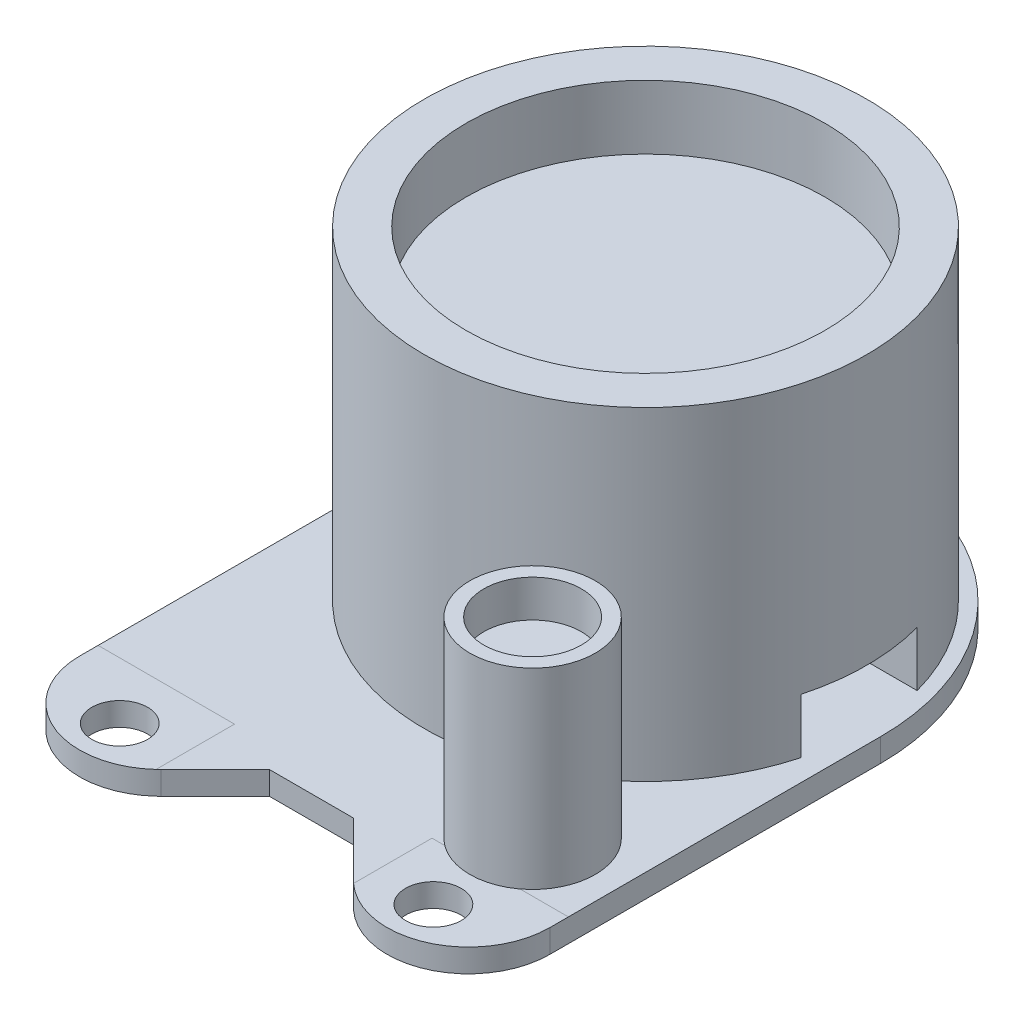
SolidWorks part; units mm, degrees
ref_plane "Front" through (0, 0, 0) normal (0, 0, 1) x (1, 0, 0)
ref_plane "Top" through (0, 0, 0) normal (0, 1, 0) x (1, 0, 0)
ref_plane "Right" through (0, 0, 0) normal (1, 0, 0) x (0, 0, -1)
sketch "Sketch1" plane through (0, 0, 0) normal (0, 1, 0) x (1, 0, 0)
  line L0 (-10.12, 0) -> (-10.12, -14.24)
  line L1 (10.12, 0) -> (10.12, -14.24)
  line L2 (-6.62, -17.74) -> (6.62, -17.74) construction
  line L3 (0, -0.8108) -> (0, -50000.8108) construction
  line L4 (-1.8103, -14.38) -> (1.8103, -14.38)
  line L5 (-4.1451, -16.7149) -> (-1.8103, -14.38)
  line L6 (1.8103, -14.38) -> (4.1451, -16.7149)
  arc A0 (10.12, 0) -> (-10.12, 0) centre (0, 0) ccw
  circle A1 centre (-6.75, -15.88) radius 1.2
  circle A2 centre (6.75, -15.88) radius 1.2
  arc A3 (-4.1451, -16.7149) -> (-10.12, -14.24) centre (-6.62, -14.24) cw
  arc A4 (4.1451, -16.7149) -> (10.12, -14.24) centre (6.62, -14.24) ccw
  dimension "D1" = 20.24
  dimension "D2" = 27.86
  dimension "D3" = 2.4
  dimension "D4" = 13.5
  dimension "D7" = 26
  dimension "D6" = 0.66
  dimension "D8" = 3.5
  dimension "D9" = 3.5
  dimension "D5" = 24.5
  dimension "D10" = 45
extrude "Boss-Extrude1" add sketch "Sketch1" along normal blind 1
sketch "Sketch2" plane through (0, 1, 0) normal (0, 1, 0) x (1, 0, 0)
  line L0 (0, 0) -> (0, -50000) construction
  line L1 (0, 0) -> (50000, 0) construction
  line L3 (10.12, -14.24) -> (10.12, 0) construction
  line L4 (-4.25, -13.44) -> (-10.12, -13.44)
  line L5 (10.12, -14.24) -> (10.12, -13.44)
  line L6 (4.25, -13.44) -> (4.25, -16.8155)
  line L7 (4.25, -13.44) -> (10.12, -13.44)
  line L8 (-4.25, -13.44) -> (-4.25, -16.8155)
  line L9 (-10.12, -14.24) -> (-10.12, -13.44)
  arc A0 (4.1451, -16.7149) -> (10.12, -14.24) centre (6.62, -14.24) ccw construction
  arc A1 (4.25, -16.8155) -> (10.12, -14.24) centre (6.62, -14.24) ccw
  arc A2 (-4.25, -16.8155) -> (-10.12, -14.24) centre (-6.62, -14.24) cw
  dimension "D2" = 4.3
  dimension "D1" = 8.5
split line "Split Line1"
sketch "Sketch3" plane through (0, 0, 0) normal (0, -1, 0) x (1, 0, 0)
  line L0 (0, 0) -> (50000, 0) construction
  line L1 (0, 0) -> (3.75, 0) construction
  line L2 (0, 0) -> (2.6517, -2.6517) construction
  circle A0 centre (0, 0) radius 4.25
  circle A1 centre (0, 0) radius 3.75 construction
  circle A3 centre (3.75, 0) radius 0.15
  circle A4 centre (2.6517, -2.6517) radius 0.15
  circle A5 centre (0, -3.75) radius 0.15
  circle A6 centre (-2.6517, -2.6517) radius 0.15
  circle A7 centre (-3.75, 0) radius 0.15
  circle A8 centre (-2.6517, 2.6517) radius 0.15
  circle A9 centre (0, 3.75) radius 0.15
  circle A10 centre (2.6517, 2.6517) radius 0.15
  dimension "D1" = 8.5
  dimension "D2" = 7.5
  dimension "D3" = 0.3
  dimension "D5" = 45
  dimension "D4" = 8
split line "Split Line2"
sketch "Sketch4" plane through (0, 1, 0) normal (0, 1, 0) x (1, 0, 0)
  circle A0 centre (0, 0) radius 9.525
  circle A1 centre (0, 0) radius 7.725
  dimension "D1" = 19.05
  dimension "D2" = 1.8
extrude "Boss-Extrude2" add sketch "Sketch4" along normal blind 13.94 separate body
sketch "Sketch5" plane through (0, 0, 0) normal (1, 0, 0) x (0, 0, -1)
  line L0 (0, 11.4963) -> (0, -49988.5037) construction
  line L2 (0, 14.94) -> (0, 1) construction
  line L3 (-13.44, 1) -> (0, 1) construction
  line L4 (-2.5, 1) -> (2.5, 1)
  line L5 (-2.5, 1) -> (-2.5, 3.36)
  line L6 (-2.5, 3.36) -> (2.5, 3.36)
  line L7 (2.5, 1) -> (2.5, 3.36)
  dimension "D1" = 5
  dimension "D2" = 2.36
extrude "Cut-Extrude1" cut sketch "Sketch5" against normal through all both and the other way through all
sketch "Sketch6" plane through (0, 14.94, 0) normal (0, 1, 0) x (1, 0, 0)
  circle A0 centre (0, 0) radius 7.725 construction
  circle A1 centre (0, 0) radius 7.725
extrude "Boss-Extrude3" add sketch "Sketch6" against normal up to surface (8.83 mm away) from offset 2.75 separate body up to face at (-8.4376, 3.36, 0) offset against normal yes
sketch "Sketch7" plane through (0, 1, 0) normal (0, 1, 0) x (1, 0, 0)
  line L0 (10.12, -13.44) -> (10.12, 0) construction
  circle A0 centre (6.42, -11.28) radius 2.7
  arc A1 (4.25, -16.8155) -> (10.12, -14.24) centre (6.62, -14.24) ccw construction
  dimension "D1" = 5.4
  dimension "D2" = 3.7
  dimension "D3" = 3.76
extrude "Extrude-Thin1" add sketch "Sketch7" along normal blind 8.25 separate body thin thin type one direction reverse wall 0.6
sketch "Sketch8" plane through (0, 9.25, 0) normal (0, 1, 0) x (1, 0, 0)
  circle A0 centre (6.42, -11.28) radius 2.1 construction
  circle A3 centre (6.42, -11.28) radius 2.1
extrude "Boss-Extrude4" add sketch "Sketch8" against normal up to surface (6.65 mm away) from offset 1.6 up to face at (0, 1, 11.6218) offset against normal yes
sketch "Sketch9" plane through (0, 1, 0) normal (0, -1, 0) x (1, 0, 0)
  circle A0 centre (0, 0) radius 4
  dimension "D1" = 8
extrude "Cut-Extrude2" cut sketch "Sketch9" against normal blind 6.45
fillet "Fillet1" radius 4 1 edges at (0, 7.45, -4)
sketch "Sketch10" plane through (0, 1, 0) normal (0, -1, 0) x (1, 0, 0)
  line L0 (7.3093, -2.5) -> (9.1911, -2.5) construction
  line L1 (7.3093, 2.5) -> (9.1911, 2.5) construction
  line L2 (-7.3093, -2.5) -> (-3.1225, -2.5)
  line L3 (-7.3093, 2.5) -> (-3.1225, 2.5)
  line L4 (3.1225, 2.5) -> (7.3093, 2.5)
  line L5 (3.1225, -2.5) -> (7.3093, -2.5)
  arc A0 (-7.3093, -2.5) -> (7.3093, -2.5) centre (0, 0) ccw construction
  arc A1 (7.3093, 2.5) -> (-7.3093, 2.5) centre (0, 0) ccw construction
  arc A2 (-7.3093, -2.5) -> (7.3093, -2.5) centre (0, 0) ccw
  arc A3 (7.3093, 2.5) -> (-7.3093, 2.5) centre (0, 0) ccw
  circle A4 centre (0, 0) radius 4 construction
  arc A5 (-3.1225, -2.5) -> (3.1225, -2.5) centre (0, 0) ccw
  arc A6 (3.1225, 2.5) -> (-3.1225, 2.5) centre (0, 0) ccw
extrude "Boss-Extrude5" add sketch "Sketch10" against normal up to surface (2.36 mm away) up to face at (0, 3.36, 4)
